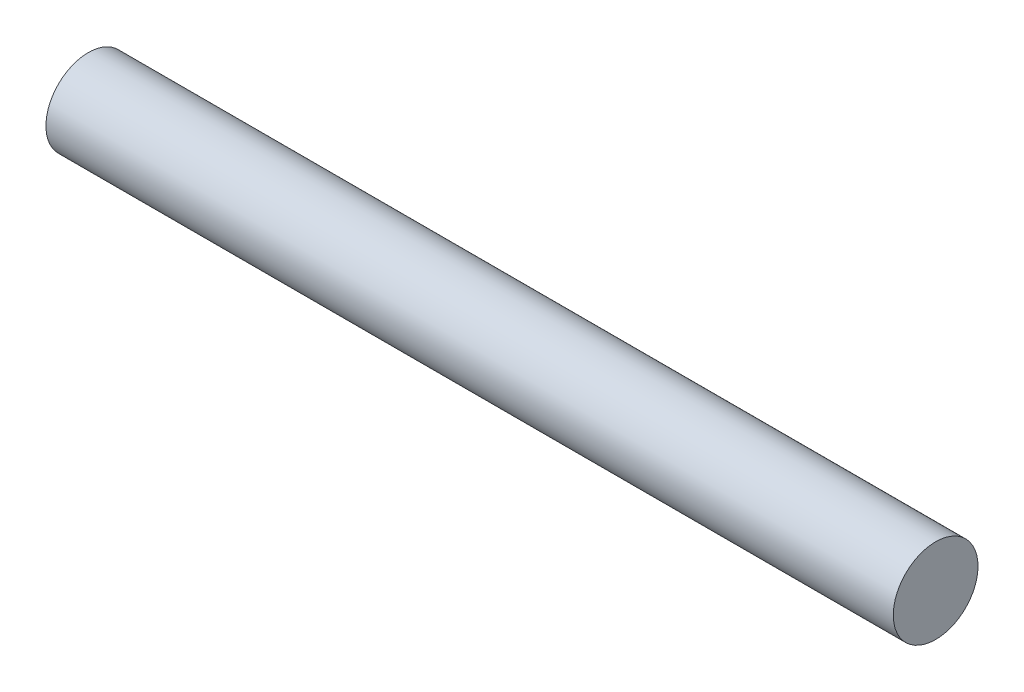
SolidWorks part; units mm, degrees
material "6061-T6 (SS)"
ref_plane "Front Plane" through (0, 0, 0) normal (0, 0, 1) x (1, 0, 0)
ref_plane "Top Plane" through (0, 0, 0) normal (0, 1, 0) x (1, 0, 0)
ref_plane "Right Plane" through (0, 0, 0) normal (1, 0, 0) x (0, 0, -1)
sketch "Sketch1" plane through (0, 0, 0) normal (1, 0, 0) x (0, 0, -1)
  circle A0 centre (0, 0) radius 15.24
  dimension "D1" = 30.48
extrude "Boss-Extrude1" add sketch "Sketch1" along normal blind 304.8
